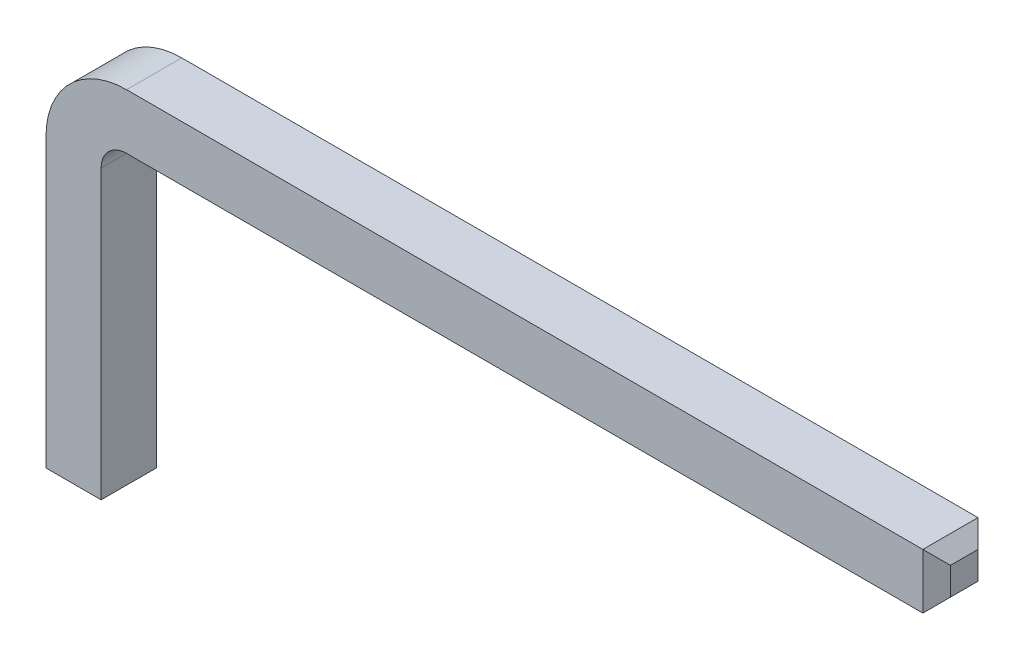
SolidWorks part; units mm, degrees
ref_plane "Front" through (0, 0, 0) normal (0, 0, 1) x (1, 0, 0)
ref_plane "Top" through (0, 0, 0) normal (0, 1, 0) x (1, 0, 0)
ref_plane "Right" through (0, 0, 0) normal (1, 0, 0) x (0, 0, -1)
sketch "Sketch1" plane through (0, 0, 0) normal (0, 0, 1) x (1, 0, 0)
  line L0 (0, 3.55) -> (0, 0)
  line L1 (0.95, 4.5) -> (10.5, 4.5)
  line L2 (10.5, 4.5) -> (10.5, 3.85)
  line L3 (0, 0) -> (0.65, 0)
  line L4 (0.95, 3.85) -> (10.5, 3.85)
  line L5 (0.65, 3.55) -> (0.65, 0)
  arc A0 (0.65, 3.55) -> (0.95, 3.85) centre (0.95, 3.55) cw
  arc A1 (0, 3.55) -> (0.95, 4.5) centre (0.95, 3.55) cw
extrude "Body" add sketch "Sketch1" along normal blind 0.65
chamfer "Chamfer" distance 0.1625 angle 45
